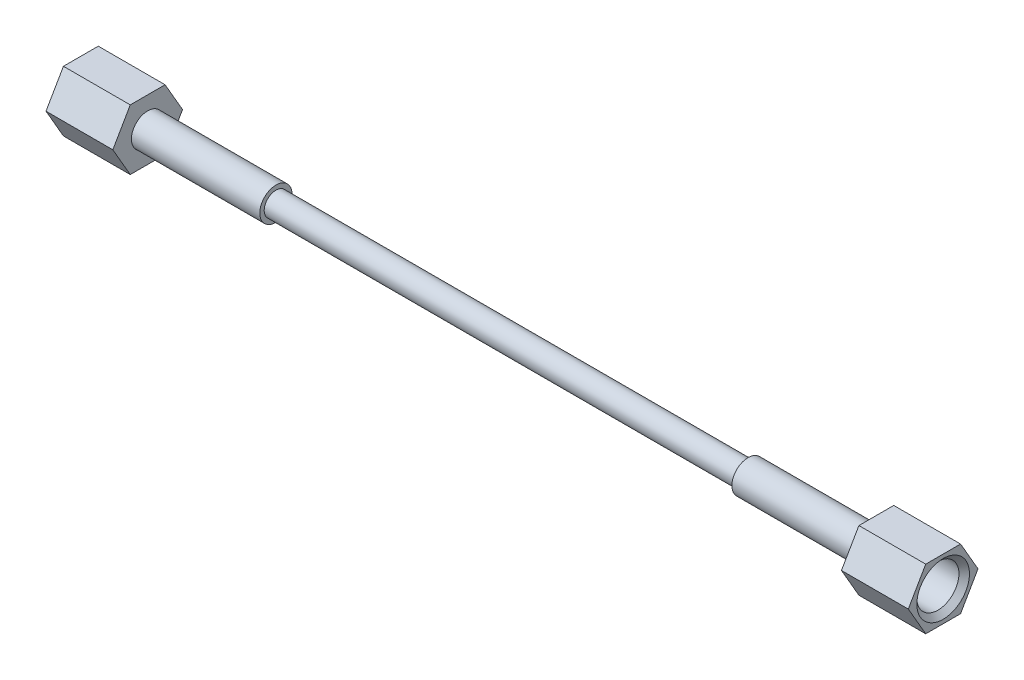
SolidWorks part; units mm, degrees
material "Alloy Steel"
ref_plane "Front Plane" through (0, 0, 0) normal (0, 0, 1) x (1, 0, 0)
ref_plane "Top Plane" through (0, 0, 0) normal (0, 1, 0) x (1, 0, 0)
ref_plane "Right Plane" through (0, 0, 0) normal (1, 0, 0) x (0, 0, -1)
ref_plane "Plane5" through (-6.858, 0, 0) normal (1, 0, 0) x (0, 0, -1)
sketch "Sketch5" plane through (-6.858, 0, 0) normal (1, 0, 0) x (0, 0, -1)
  line L0 (4.1061, 7.112) -> (-4.1061, 7.112)
  line L1 (-4.1061, 7.112) -> (-8.2122, 0)
  line L2 (-8.2122, 0) -> (-4.1061, -7.112)
  line L3 (-4.1061, -7.112) -> (4.1061, -7.112)
  line L4 (4.1061, -7.112) -> (8.2122, 0)
  line L5 (8.2122, 0) -> (4.1061, 7.112)
extrude "Extrude2" add sketch "Sketch5" along normal blind 15.748 separate body
hole_wizard "Hole2" positions "Sketch7" profile "Sketch6" legacy end condition up to next
sketch "Sketch7" plane through (8.89, 0, 0) normal (1, 0, 0) x (0, 0, -1)
  point P0 (0, 0)
sketch "Sketch6" plane through (8.89, 0, 0) normal (0, 1, 0) x (0, 0, -1)
  line L0 (0, 0) -> (0, 15.748)
  line L1 (0, 15.748) -> (3.8354, 15.748)
  line L2 (3.8354, 15.748) -> (3.8354, 9.5661)
  line L3 (3.8354, 9.5661) -> (4.9606, 8.89)
  line L4 (4.9606, 8.89) -> (4.9606, 0)
  line L5 (4.9606, 0) -> (0, 0)
  line L6 (0, -6.13) -> (0, 109.2824) construction
  line L7 (-3.8354, 9.5661) -> (-4.9606, 8.89) construction
  line L8 (0, 15.748) -> (-3.8354, 15.748) construction
  dimension "Diameter" = 7.6708
  dimension "Depth" = 15.748
  dimension "C-Drill Diameter" = 9.9212
  dimension "C-Drill Depth" = 8.89
  dimension "C-Drill Angle" = 118
chamfer "Chamfer2" distance 1.2402 angle 45 1 edges at (8.89, 0, -4.9606)
ref_plane "Plane4" through (0, 0, 0) normal (0, 0, -1) x (-1, 0, 0)
sketch "Sketch8" plane through (0, 0, 0) normal (0, 0, -1) x (-1, 0, 0)
  line L0 (0.6914, 3.81) -> (2.3854, 0.9906)
  line L1 (2.3854, 0.9906) -> (183.0346, 0.9906)
  line L2 (148.336, 3.81) -> (184.7286, 3.81)
  line L3 (148.336, 2.7686) -> (148.336, 3.81)
  line L4 (184.7286, 3.81) -> (183.0346, 0.9906)
  line L5 (148.336, 2.7686) -> (37.084, 2.7686)
  line L6 (37.084, 2.7686) -> (37.084, 3.81)
  line L7 (37.084, 3.81) -> (0.6914, 3.81)
  line L8 (0.6914, 0) -> (202.5086, 0) construction
  line L9 (92.71, 24.5048) -> (92.71, -25.5618) construction
  line L10 (6.858, 7.112) -> (6.858, 0) construction
  line L13 (0.6761, 3.8354) -> (0, 4.9606) construction
  dimension "D1" = 101.6
  dimension "D2" = 1.9812
  dimension "D3" = 5.5372
  dimension "D4" = 7.62
  dimension "D6" = 30.226
revolve "Revolve2" add sketch "Sketch8" angle 360 about L8
ref_plane "Plane6" through (-92.71, 0, 0) normal (1, 0, 0) x (0, 0, -1)
mirror "Mirror2" about plane through (-92.71, 0, 0) normal (1, 0, 0) of bodies 118
